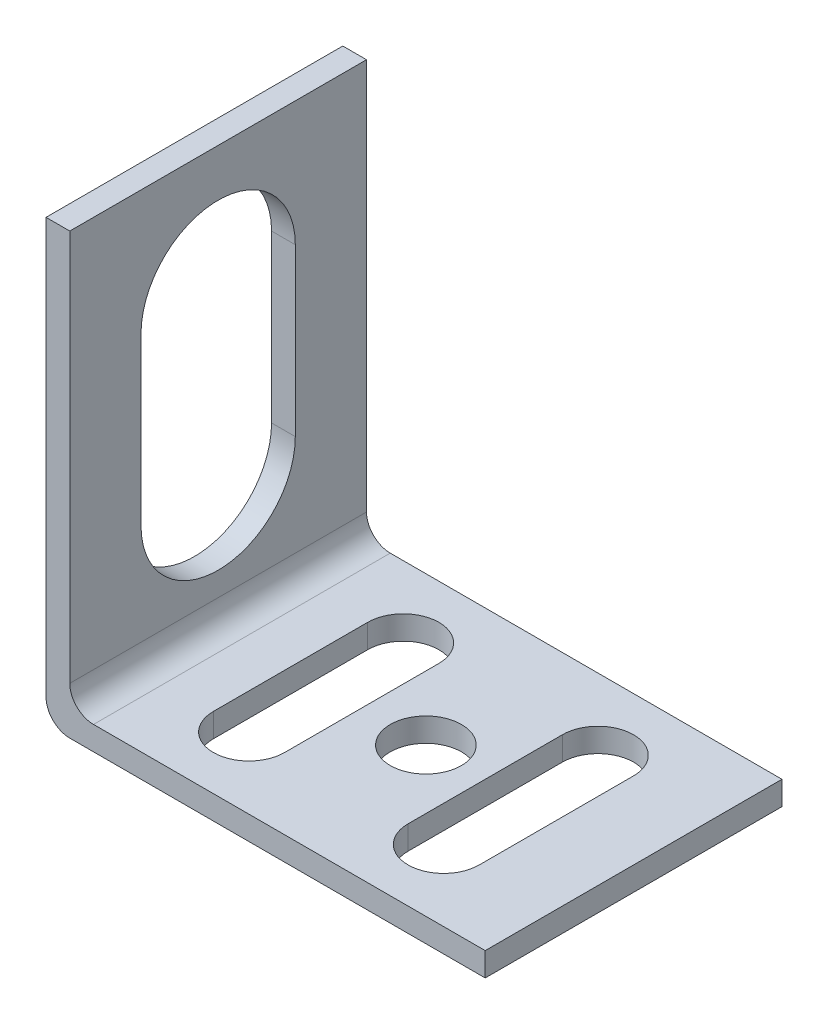
SolidWorks part; units mm, degrees
ref_plane "Alzado" through (0, 0, 0) normal (0, 0, 1) x (1, 0, 0)
ref_plane "Planta" through (0, 0, 0) normal (0, 1, 0) x (1, 0, 0)
ref_plane "Vista lateral" through (0, 0, 0) normal (1, 0, 0) x (0, 0, -1)
sketch "Sketch1" plane through (0, 0, 0) normal (0, 0, 1) x (1, 0, 0)
  line L4 (-19.0993, 23.4592) -> (-19.0993, -11.5408)
  line L5 (-17.0993, -13.5408) -> (17.9007, -13.5408)
  line L6 (-19.0993, 23.4592) -> (-17.0993, 23.4592)
  line L7 (-17.0993, 23.4592) -> (-17.0993, -9.5408)
  line L8 (-15.0993, -11.5408) -> (17.9007, -11.5408)
  line L9 (17.9007, -11.5408) -> (17.9007, -13.5408)
  arc A1 (-17.0993, -13.5408) -> (-19.0993, -11.5408) centre (-17.0993, -11.5408) cw
  arc A2 (-15.0993, -11.5408) -> (-17.0993, -9.5408) centre (-15.0993, -9.5408) cw
  dimension "D1" = 2
extrude "Boss-Extrude1" add sketch "Sketch1" along normal blind 25
sketch "Sketch2" plane through (-19.0993, 0, 0) normal (-1, 0, 0) x (0, 0, 1)
  line L3 (12.5, -1.0408) -> (12.5, 12.9592) construction
  line L4 (6, -1.0408) -> (6, 12.9592)
  line L5 (19, -1.0408) -> (19, 12.9592)
  arc A0 (6, -1.0408) -> (19, -1.0408) centre (12.5, -1.0408) ccw
  arc A1 (19, 12.9592) -> (6, 12.9592) centre (12.5, 12.9592) ccw
  point P8 (12.5, 5.9592)
extrude "Cut-Extrude1" cut sketch "Sketch2" against normal blind 25
sketch "Sketch3" plane through (0, -13.5408, 0) normal (0, -1, 0) x (1, 0, 0)
  line L0 (8.4007, 6) -> (8.4007, 19) construction
  line L1 (5.4007, 6) -> (5.4007, 19)
  line L2 (11.4007, 6) -> (11.4007, 19)
  line L4 (-8.002, 6) -> (-8.002, 19) construction
  line L5 (-11.002, 6) -> (-11.002, 19)
  line L6 (-5.002, 6) -> (-5.002, 19)
  circle A0 centre (0.4007, 12.5) radius 3
  arc A1 (-11.002, 6) -> (-5.002, 6) centre (-8.002, 6) ccw
  arc A2 (-5.002, 19) -> (-11.002, 19) centre (-8.002, 19) ccw
  arc A3 (5.4007, 6) -> (11.4007, 6) centre (8.4007, 6) ccw
  arc A4 (11.4007, 19) -> (5.4007, 19) centre (8.4007, 19) ccw
  point P5 (8.4007, 12.5)
  point P12 (-8.002, 12.5)
extrude "Cut-Extrude2" cut sketch "Sketch3" against normal blind 25
